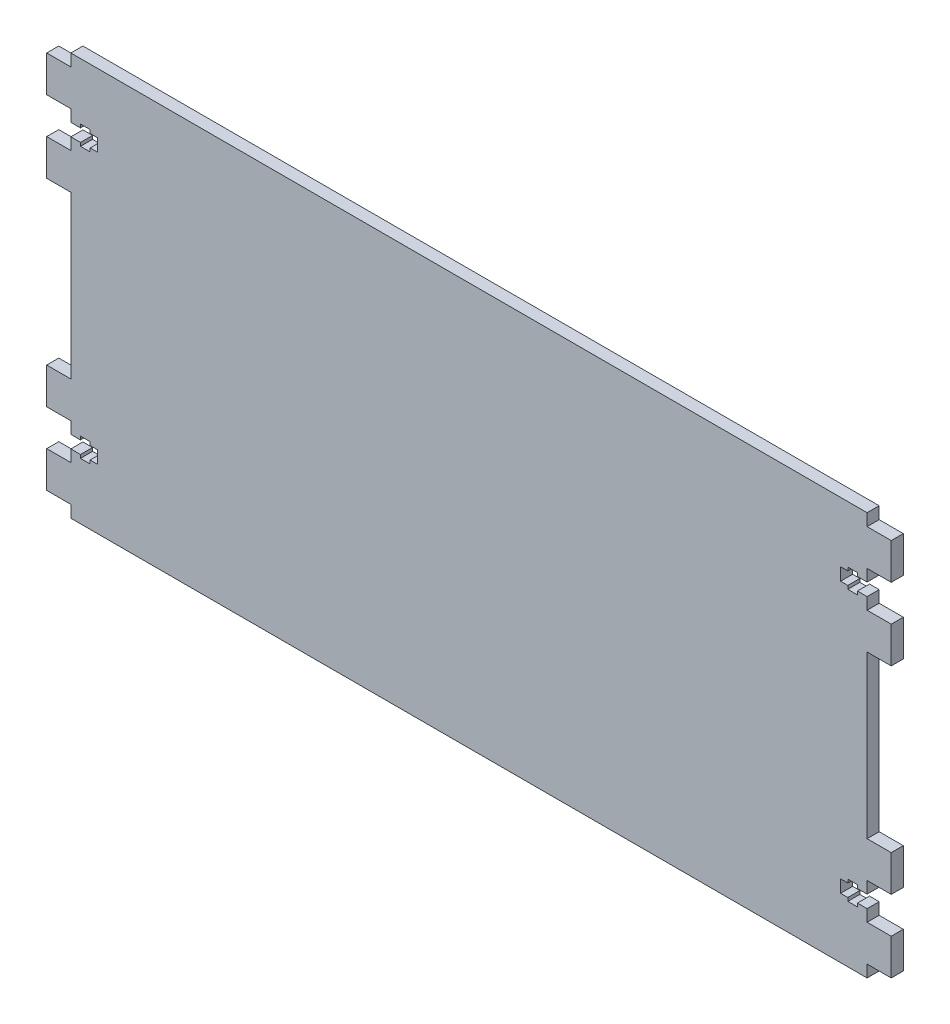
SolidWorks part; units mm, degrees
ref_plane "Front Plane" through (0, 0, 0) normal (0, 0, 1) x (1, 0, 0)
ref_plane "Top Plane" through (0, 0, 0) normal (0, 1, 0) x (1, 0, 0)
ref_plane "Right Plane" through (0, 0, 0) normal (1, 0, 0) x (0, 0, -1)
sketch "Sketch1" plane through (0, 0, 0) normal (0, 0, 1) x (1, 0, 0)
  line L1 (-165, -83.5) -> (165, -83.5)
  line L2 (-165, -83.5) -> (-165, 83.5)
  line L3 (-165, 83.5) -> (165, 83.5)
  line L4 (165, -83.5) -> (165, 83.5)
  line L5 (-165, -83.5) -> (165, 83.5) construction
  line L6 (-165, 83.5) -> (165, -83.5) construction
  point P0 (0, 0)
  dimension "D1" = 330
  dimension "D2" = 167
extrude "Boss-Extrude1" add sketch "Sketch1" along normal mid plane 5
sketch "Sketch2" plane through (-165, 0, 0) normal (-1, 0, 0) x (0, 0, 1)
  line L0 (-2.5, 83.5) -> (-2.5, -83.5) construction
  line L1 (-2.5, 78.5) -> (2.5, 78.5)
  line L2 (-2.5, 78.5) -> (-2.5, 63.5)
  line L3 (-2.5, 63.5) -> (2.5, 63.5)
  line L4 (2.5, 78.5) -> (2.5, 63.5)
  line L5 (2.5, 83.5) -> (2.5, -83.5) construction
  line L6 (2.5, 83.5) -> (-2.5, 83.5) construction
  line L7 (-2.5, 48.5) -> (2.5, 48.5)
  line L8 (-2.5, 48.5) -> (-2.5, 33.5)
  line L9 (-2.5, 33.5) -> (2.5, 33.5)
  line L10 (2.5, 48.5) -> (2.5, 33.5)
  point P12 (0, 83.5)
  dimension "D1" = 5
  dimension "D2" = 15
  dimension "D3" = 15
  dimension "D4" = 15
extrude "Boss-Extrude2" add sketch "Sketch2" along normal blind 10
sketch "Sketch4" plane through (0, 0, 2.5) normal (0, 0, 1) x (1, 0, 0)
  line L0 (-1165, 56) -> (48835, 56) construction
  line L1 (-165, 63.5) -> (-165, 48.5) construction
  line L3 (-154, 53.4) -> (-165, 53.4)
  line L4 (-154, 53.4) -> (-154, 58.6)
  line L5 (-154, 58.6) -> (-165, 58.6)
  line L6 (-165, 53.4) -> (-165, 58.6)
  line L7 (-154, 53.4) -> (-165, 58.6) construction
  line L8 (-154, 58.6) -> (-165, 53.4) construction
  point P1 (-159.5, 56)
  point P5 (-165, 56)
  dimension "D1" = 5.2
  dimension "D2" = 11
extrude "Cut-Extrude1" cut sketch "Sketch4" against normal through all
sketch "Sketch5" plane through (0, 0, 2.5) normal (0, 0, 1) x (1, 0, 0)
  line L0 (-1145, 56) -> (48855, 56) construction
  line L1 (-154, 53.4) -> (-154, 58.6) construction
  line L3 (-161, 52) -> (-157, 52)
  line L4 (-161, 52) -> (-161, 60)
  line L5 (-161, 60) -> (-157, 60)
  line L6 (-157, 52) -> (-157, 60)
  line L7 (-161, 52) -> (-157, 60) construction
  line L8 (-161, 60) -> (-157, 52) construction
  point P1 (-159, 56)
  point P5 (-154, 56)
  dimension "D1" = 8
  dimension "D2" = 4
  dimension "D3" = 5
extrude "Cut-Extrude2" cut sketch "Sketch5" against normal through all
mirror "Mirror1" about plane through (0, 0, 0) normal (0, 1, 0) of "Cut-Extrude2", "Cut-Extrude1", "Boss-Extrude2"
mirror "Mirror2" about plane through (0, 0, 0) normal (1, 0, 0) of "Mirror1", "Boss-Extrude2", "Cut-Extrude1", "Cut-Extrude2"
